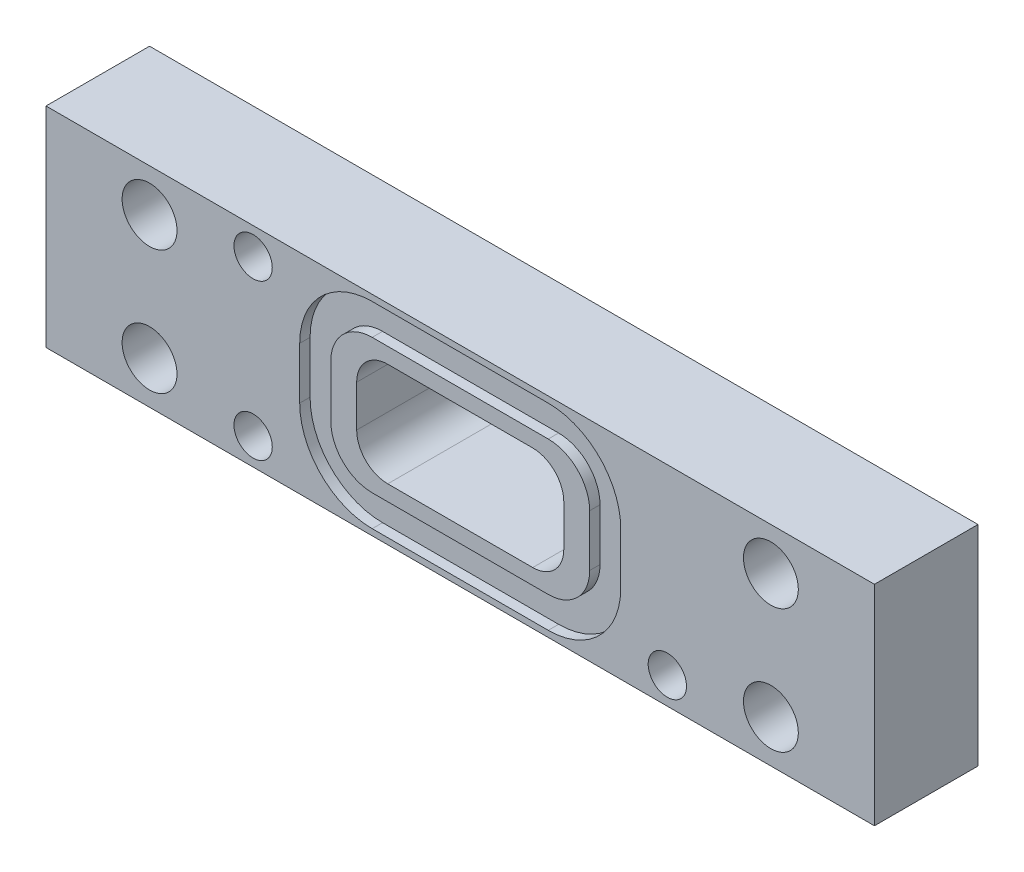
SolidWorks part; units mm, degrees
material "ABS PC"
ref_plane "Ebene vorne" through (0, 0, 0) normal (0, 0, 1) x (1, 0, 0)
ref_plane "Ebene oben" through (0, 0, 0) normal (0, 1, 0) x (1, 0, 0)
ref_plane "Ebene rechts" through (0, 0, 0) normal (1, 0, 0) x (0, 0, -1)
sketch "Skizze1" plane through (0, 0, 0) normal (0, 0, 1) x (1, 0, 0)
  line L0 (0, 10.1) -> (80, 10.1) construction
  line L1 (0, 0) -> (80, 0)
  line L2 (0, 0) -> (0, 20.2)
  line L3 (0, 20.2) -> (80, 20.2)
  line L4 (80, 0) -> (80, 20.2)
  line L5 (40, 20.2) -> (40, 0) construction
  line L7 (30, 15.1) -> (50, 15.1)
  line L8 (30, 15.1) -> (30, 5.1)
  line L9 (30, 5.1) -> (50, 5.1)
  line L10 (50, 15.1) -> (50, 5.1)
  line L11 (30, 15.1) -> (50, 5.1) construction
  line L12 (30, 5.1) -> (50, 15.1) construction
  line L13 (70, 4.1) -> (10, 4.1) construction
  line L14 (70, 4.1) -> (70, 16.1) construction
  line L15 (70, 16.1) -> (10, 16.1) construction
  line L16 (10, 4.1) -> (10, 16.1) construction
  line L17 (70, 4.1) -> (10, 16.1) construction
  line L18 (70, 16.1) -> (10, 4.1) construction
  circle A0 centre (10, 16.1) radius 2.65
  circle A1 centre (10, 4.1) radius 2.65
  circle A2 centre (70, 16.1) radius 2.65
  circle A3 centre (70, 4.1) radius 2.65
  point P9 (40, 10.1)
  point P14 (40, 10.1)
  dimension "D7" = 5.3
  dimension "D1" = 20.2
  dimension "D2" = 80
  dimension "D3" = 10
  dimension "D4" = 20
  dimension "D5" = 12
  dimension "D6" = 60
extrude "Aufsatz-Linear austragen1" add sketch "Skizze1" along normal blind 10
fillet "Verrundung1" radius 3 4 edges at (50, 5.1, 5) (30, 5.1, 5) (50, 15.1, 5) (30, 15.1, 5)
hole_wizard "Ø3.7 (3.7) Durchmesser Bohrung1" positions "Skizze5" profile "Skizze6" hole size "Ø3.7" standard "DIN" end condition through all
sketch "Skizze5" plane through (0, 0, 10) normal (0, 0, 1) x (1, 0, 0)
  line L0 (20, 17.6) -> (60, 2.6) construction
  line L2 (20, 2.6) -> (60, 17.6) construction
  line L4 (40, 20.2) -> (40, 0) construction
  line L5 (80, 20.2) -> (0, 20.2) construction
  line L6 (0, 0) -> (80, 0) construction
  line L8 (0, 10.1) -> (80, 10.1) construction
  line L9 (0, 20.2) -> (0, 0) construction
  line L10 (80, 0) -> (80, 20.2) construction
  point P0 (20, 17.6)
  point P2 (20, 2.6)
  point P4 (60, 2.6)
  point P19 (40, 10.1)
  point P35 (40, 10.1)
  dimension "D2" = 15
sketch "Skizze6" plane through (20, 17.6, 10) normal (1, 0, 0) x (0, -1, 0)
  line L0 (0, 0) -> (0, 10)
  line L1 (0, 10) -> (1.85, 10)
  line L2 (1.85, 10) -> (1.85, 0)
  line L5 (1.85, 0) -> (0, 0)
  line L11 (0, -6.35) -> (0, 107.95) construction
  dimension "Bohrerdurchmesser" = 3.7
  dimension "Bohrungstiefe" = 10
sketch "Skizze7" plane through (0, 0, 10) normal (0, 0, 1) x (1, 0, 0)
  line L0 (47, 15.1) -> (33, 15.1) construction
  line L1 (31.5, 16.6) -> (48.5, 16.6)
  line L2 (27.5, 12.6) -> (27.5, 7.6)
  line L3 (31.5, 3.6) -> (48.5, 3.6)
  line L4 (52.5, 12.6) -> (52.5, 7.6)
  line L5 (27.5, 16.6) -> (52.5, 3.6) construction
  line L6 (27.5, 3.6) -> (52.5, 16.6) construction
  line L7 (30, 12.1) -> (30, 8.1) construction
  line L8 (24.5, 12.6) -> (24.5, 7.6)
  line L9 (31.5, 0.6) -> (48.5, 0.6)
  line L10 (55.5, 12.6) -> (55.5, 7.6)
  line L11 (31.5, 19.6) -> (48.5, 19.6)
  arc A0 (48.5, 16.6) -> (52.5, 12.6) centre (48.5, 12.6) cw
  arc A1 (48.5, 3.6) -> (52.5, 7.6) centre (48.5, 7.6) ccw
  arc A2 (27.5, 7.6) -> (31.5, 3.6) centre (31.5, 7.6) ccw
  arc A3 (31.5, 16.6) -> (27.5, 12.6) centre (31.5, 12.6) ccw
  arc A4 (31.5, 19.6) -> (24.5, 12.6) centre (31.5, 12.6) ccw
  arc A5 (24.5, 7.6) -> (31.5, 0.6) centre (31.5, 7.6) ccw
  arc A6 (48.5, 0.6) -> (55.5, 7.6) centre (48.5, 7.6) ccw
  arc A7 (48.5, 19.6) -> (55.5, 12.6) centre (48.5, 12.6) cw
  point P0 (40, 10.1)
  point P5 (0, 0)
  point P8 (0, 0)
  point P9 (0, 0)
  point P10 (0, 0)
  point P11 (40, 15.1)
  point P12 (0, 0)
  point P15 (30, 10.1)
  dimension "D3" = 4
  dimension "D1" = 25
  dimension "D2" = 1.5
  dimension "D4" = 3
extrude "Schnitt-Linear austragen1" cut sketch "Skizze7" against normal blind 1
